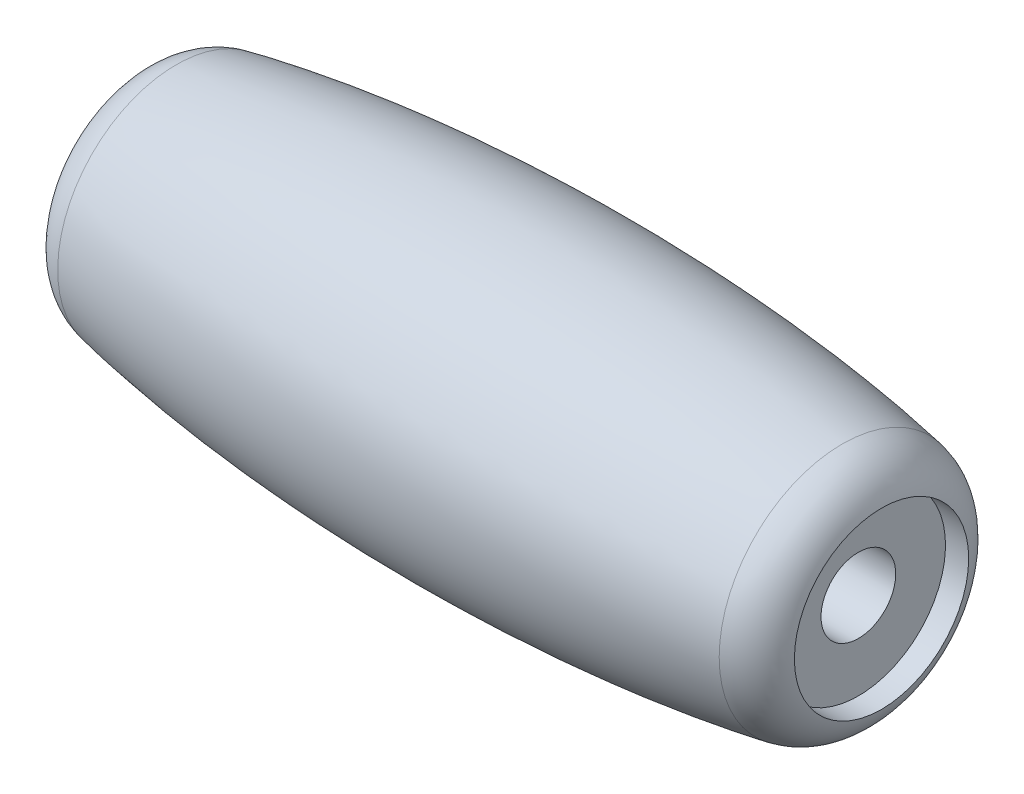
SolidWorks part; units mm, degrees
ref_plane "Ön Düzlem" through (0, 0, 0) normal (0, 0, 1) x (1, 0, 0)
ref_plane "Üst Düzlem" through (0, 0, 0) normal (0, 1, 0) x (1, 0, 0)
ref_plane "Sağ Düzlem" through (0, 0, 0) normal (1, 0, 0) x (0, 0, -1)
sketch "Sketch1" plane through (0, 0, 0) normal (0, 0, 1) x (1, 0, 0)
  line L0 (-15.4739, 0) -> (14.5261, 0) construction
  line L1 (-15.4739, 0) -> (14.5261, 0)
  line L2 (-15.4739, 0) -> (-15.4739, 2.7963)
  line L3 (-15, 3.76) -> (15, 3.76) construction
  line L4 (14.5261, 0) -> (14.5261, 2.978)
  line L6 (-15, 3.76) -> (0, 0) construction
  line L8 (0, 0) -> (15, 3.76) construction
  arc A1 (12.8825, 4.946) -> (14.5261, 2.978) centre (12.5261, 2.978) cw
  arc A3 (-15.4739, 2.7963) -> (-13.8713, 4.7564) centre (-13.4739, 2.7963) cw
  ellipse E1 centre (0, 0) end of major axis (22.7562, 0) minor radius 6 (12.8825, 4.946) -> (-13.8713, 4.7564) ccw
  dimension "D1" = 30
  dimension "D2" = 6
revolve "Revolve5" add sketch "Sketch1" angle 360 about L1
sketch "Sketch2" plane through (14.5261, 0, 0) normal (1, 0, 0) x (0, 0, -1)
  circle A0 centre (0, 0) radius 1.5
  dimension "D1" = 3
extrude "Cut-Extrude1" cut sketch "Sketch2" against normal through all
ref_plane "Plane1" through (-0.4739, 0, 0) normal (1, 0, 0) x (0, 0, -1)
sketch "Sketch3" plane through (14.5261, 0, 0) normal (1, 0, 0) x (0, 0, -1)
  circle A0 centre (0, 0) radius 1.5
  circle A1 centre (0, 0) radius 3.5
  dimension "D1" = 7
extrude "Cut-Extrude2" cut sketch "Sketch3" against normal blind 1
mirror "Mirror1" about plane through (-0.4739, 0, 0) normal (1, 0, 0) of "Cut-Extrude2"
